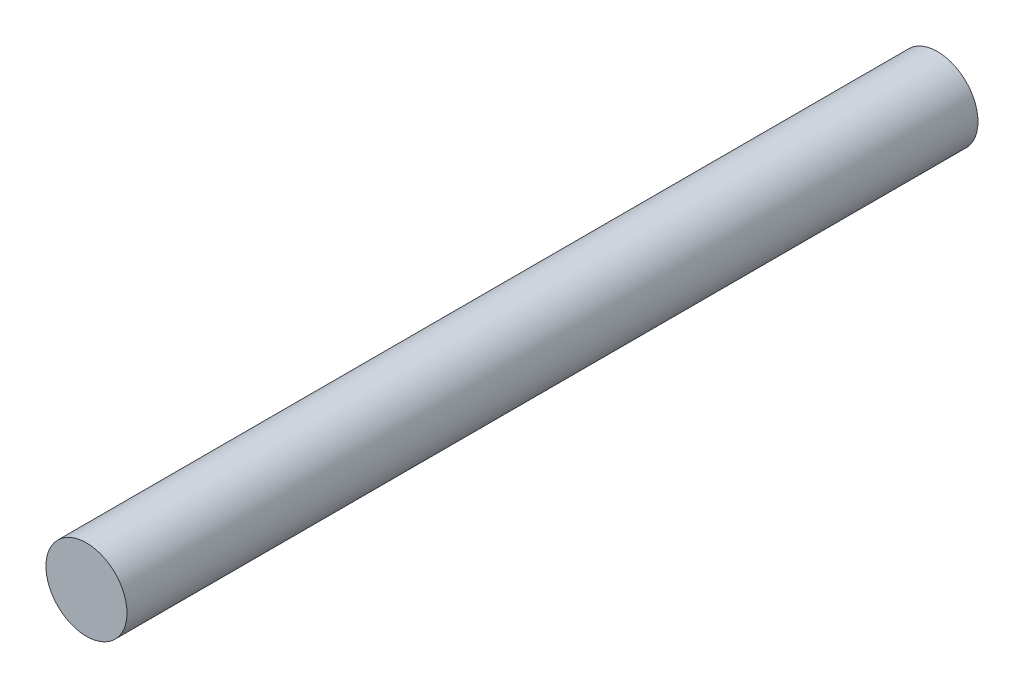
SolidWorks part; units mm, degrees
ref_plane "Front Plane" through (0, 0, 0) normal (0, 0, 1) x (1, 0, 0)
ref_plane "Top Plane" through (0, 0, 0) normal (0, 1, 0) x (1, 0, 0)
ref_plane "Right Plane" through (0, 0, 0) normal (1, 0, 0) x (0, 0, -1)
sketch "Sketch1" plane through (0, 0, 0) normal (0, 0, 1) x (1, 0, 0)
  circle A0 centre (0, 0) radius 1
  dimension "D1" = 2
extrude "Boss-Extrude1" add sketch "Sketch1" along normal mid plane 21
